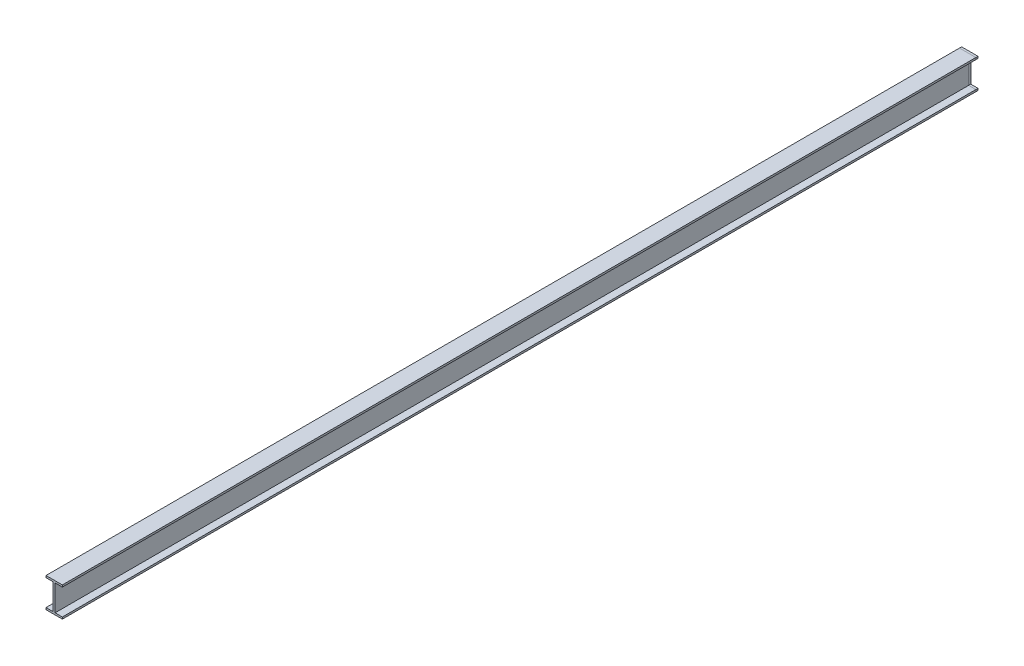
SolidWorks part; units mm, degrees
ref_plane "Front Plane" through (0, 0, 0) normal (0, 0, 1) x (1, 0, 0)
ref_plane "Top Plane" through (0, 0, 0) normal (0, 1, 0) x (1, 0, 0)
ref_plane "Right Plane" through (0, 0, 0) normal (1, 0, 0) x (0, 0, -1)
sketch "Sketch2" plane through (0, 0, 0) normal (0, 0, 1) x (1, 0, 0)
  line L0 (0, 177.8) -> (0, 0) construction
  line L1 (-49.022, 0) -> (49.022, 0)
  line L2 (0, 0) -> (0, 11.43)
  line L3 (-49.022, 11.43) -> (49.022, 11.43)
  line L4 (49.022, 0) -> (49.022, 11.43)
  line L5 (0, 11.43) -> (5.715, 11.43)
  line L6 (0, 11.43) -> (0, 166.37)
  line L7 (0, 166.37) -> (5.715, 166.37)
  line L8 (5.715, 11.43) -> (5.715, 166.37)
  line L9 (-49.022, 166.37) -> (49.022, 166.37)
  line L10 (0, 166.37) -> (0, 177.8)
  line L11 (-49.022, 177.8) -> (49.022, 177.8)
  line L12 (49.022, 166.37) -> (49.022, 177.8)
  line L13 (-49.022, 0) -> (-49.022, 11.43)
  line L14 (-5.715, 11.43) -> (-5.715, 166.37)
  line L15 (-49.022, 166.37) -> (-49.022, 177.8)
  dimension "D1" = 177.8
  dimension "D2" = 11.43
  dimension "D3" = 11.43
  dimension "D4" = 5.715
  dimension "D5" = 49.022
  dimension "D6" = 49.022
extrude "Boss-Extrude1" add sketch "Sketch2" along normal blind 5486.4 contours L15 L9 L10 L11 | L9 L12 L11 L10 L7 | L3 L8 L7 L6 | L14 L3 L6 L9 | L13 L1 L2 L3 | L1 L4 L3 L2
ref_plane "Plane1" through (0, 0, 12.7) normal (0, 0, 1) x (1, 0, 0)
split line "Split Line1"
